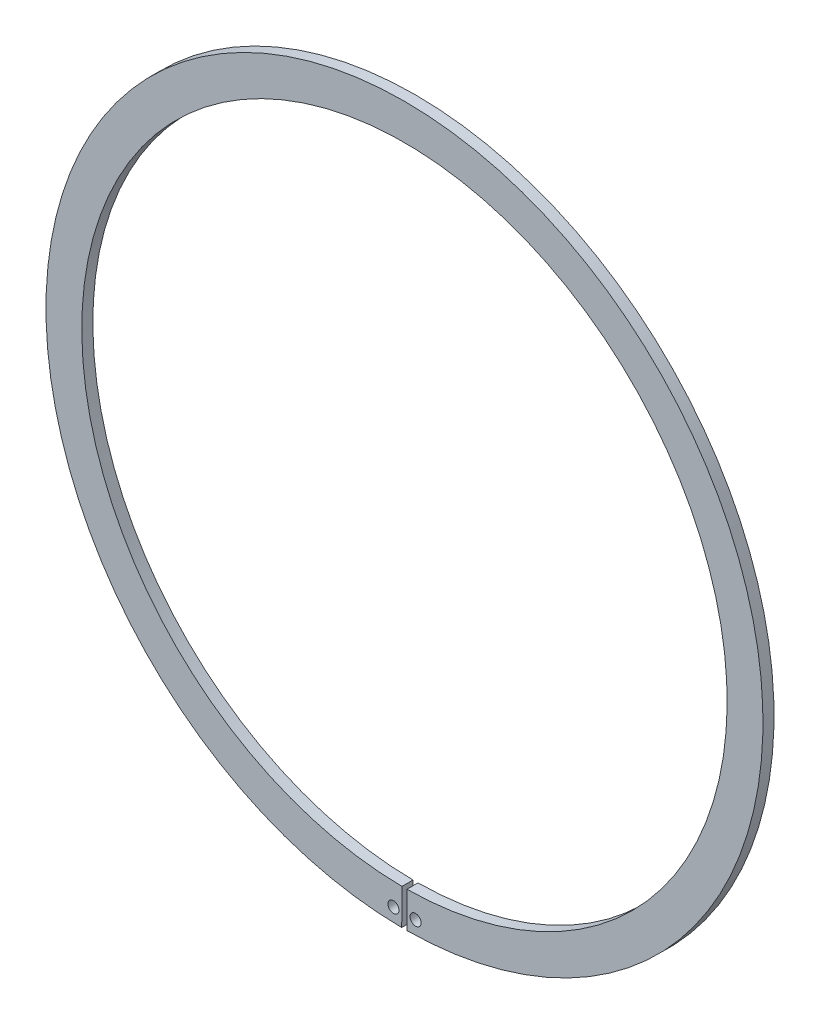
SolidWorks part; units mm, degrees
material "X 6 CrNiMoTi 17 12 2 (1.4571)"
ref_plane "Ebene vorne" through (0, 0, 0) normal (0, 0, 1) x (1, 0, 0)
ref_plane "Ebene oben" through (0, 0, 0) normal (0, 1, 0) x (1, 0, 0)
ref_plane "Ebene rechts" through (0, 0, 0) normal (1, 0, 0) x (0, 0, -1)
sketch "Clipboard" plane through (0, 0, 0) normal (0, 0, 1) x (1, 0, 0)
  line L0 (0, 0) -> (16, 0)
  line L1 (0, 0) -> (0, 8)
  line L2 (0, 0) -> (0, -16.2)
  circle A0 centre (0, 0) radius 2.5
  circle A1 centre (0, 0) radius 150
sketch "BodySke" plane through (0, 0, 0) normal (0, 0, 1) x (1, 0, 0)
  line L0 (-1.5431, 0) -> (1.5431, 0) construction
  line L1 (0, 0) -> (0, 162) construction
  line L2 (1.1252, -145.9957) -> (1.25, -162.1952)
  line L3 (-1.1252, -145.9957) -> (-1.25, -162.1952)
  line L4 (0, 0) -> (19.0874, -161.073) construction
  line L5 (0, 0) -> (-19.0874, -161.073) construction
  line L7 (10.9576, -160.0027) -> (10.7954, -161.2347)
  line L8 (-10.9576, -160.0027) -> (-10.7954, -161.2347)
  circle A0 centre (0, 0) radius 146 construction
  arc A1 (1.1252, -145.9957) -> (-1.1252, -145.9957) centre (0, 0) ccw
  arc A2 (18.1224, -152.93) -> (-18.1224, -152.93) centre (0, 4.0136) ccw construction
  arc A3 (1.25, -162.1952) -> (10.0985, -161.8853) centre (0, 0) ccw
  arc A4 (18.1456, -152.9273) -> (10.9576, -160.0027) centre (19.0874, -161.073) ccw
  arc A5 (-10.9576, -160.0027) -> (-18.1456, -152.9273) centre (-19.0874, -161.073) ccw
  arc A6 (-10.0985, -161.8853) -> (-1.25, -162.1952) centre (0, 0) ccw
  arc A7 (18.1456, -152.9273) -> (-18.1456, -152.9273) centre (0, 4.0136) ccw
  arc A8 (-11.5275, -155.6738) -> (11.5275, -155.6738) centre (0, 0) ccw construction
  circle A9 centre (5, -156.0199) radius 2.5
  circle A10 centre (-5, -156.0199) radius 2.5
  arc A11 (10.7954, -161.2347) -> (10.0985, -161.8853) centre (10.0518, -161.1368) cw
  arc A12 (-10.7954, -161.2347) -> (-10.0985, -161.8853) centre (-10.0518, -161.1368) ccw
  point P28 (10.715, -161.8457)
  point P31 (-10.715, -161.8457)
extrude "Body" add sketch "BodySke" against normal blind 5
sketch "NotSke" plane through (0, 0, 0) normal (0, 0, 1) x (1, 0, 0)
  line L0 (5, -153.5199) -> (5, -158.5199)
  line L1 (5, -158.5199) -> (-5, -158.5199)
  line L2 (-5, -158.5199) -> (-5, -153.5199)
  line L3 (-5, -153.5199) -> (5, -153.5199)
  circle A0 centre (5, -156.0199) radius 2.5 construction
  circle A1 centre (-5, -156.0199) radius 2.5 construction
extrude "Notch" [suppressed] cut sketch "NotSke" against normal through all
sketch "UnlSke" plane through (0, 0, 0) normal (0, 0, 1) x (1, 0, 0)
  line L0 (-7.7911, -162.0128) -> (-7.0129, -145.8315)
  line L1 (7.7911, -162.0128) -> (7.0129, -145.8315)
  arc A0 (7.0129, -145.8315) -> (-7.0129, -145.8315) centre (0, 0) ccw
  arc A1 (7.7911, -162.0128) -> (-7.7911, -162.0128) centre (0, 0) ccw
  arc A2 (1.25, -162.1952) -> (10.0985, -161.8853) centre (0, 0) ccw construction
  arc A3 (1.1252, -145.9957) -> (-1.1252, -145.9957) centre (0, 0) ccw construction
  circle A4 centre (-5, -156.0199) radius 2.5 construction
  circle A5 centre (5, -156.0199) radius 2.5 construction
extrude "Unlug" add sketch "UnlSke" against normal through all
equation "' \"ShaftDia@Clipboard\" = 3"
equation "' \"Thickness@Body\" = 0.4"
equation "' \"GrooveDia@BodySke\" = 2.8"
equation "' \"LugSection@Clipboard\" = 1.9"
equation "' \"LargeSection@Clipboard\" = 0.8"
equation "' \"HoleDia@Clipboard\" = 1.0"
equation "\"SmallSection@Clipboard\" = \"LargeSection@Clipboard\" * 0.5"
equation "\"Gap@BodySke\" =  \"Thickness@Body\" / 2"
equation "\"LargeRad@BodySke\" =  \"GrooveDia@BodySke\" / 2 +  \"LargeSection@Clipboard\""
equation "\"SmallRad@BodySke\" =  \"GrooveDia@BodySke\" / 2 +  \"SmallSection@Clipboard\""
equation "\"LugRad@BodySke\" = \"GrooveDia@BodySke\" / 2 + \"LugSection@Clipboard\""
equation "\"HoleOffsetRad@BodySke\" = (  \"ShaftDia@Clipboard\" / 2 + \"LugRad@BodySke\" ) / 2"
equation "\"HoleSpacing@BodySke\" = \"Gap@BodySke\"  * 2 +  \"HoleDia@Clipboard\""
equation "\"HoleDia@BodySke\" =  \"HoleDia@Clipboard\""
equation "\"SmallAngle@BodySke\" = atn(\"HoleSpacing@BodySke\" / 2 / sqr(\"HoleOffsetRad@BodySke\"  * \"HoleOffsetRad@BodySke\" - (\"HoleSpacing@BodySke\" / 2) * (\"HoleSpacing@BodySke\" / 2) ))  * 7 *  (\"LargeRad@BodySke\" / \"SmallRad@BodySke\")* ( 180 / 3.141593)"
